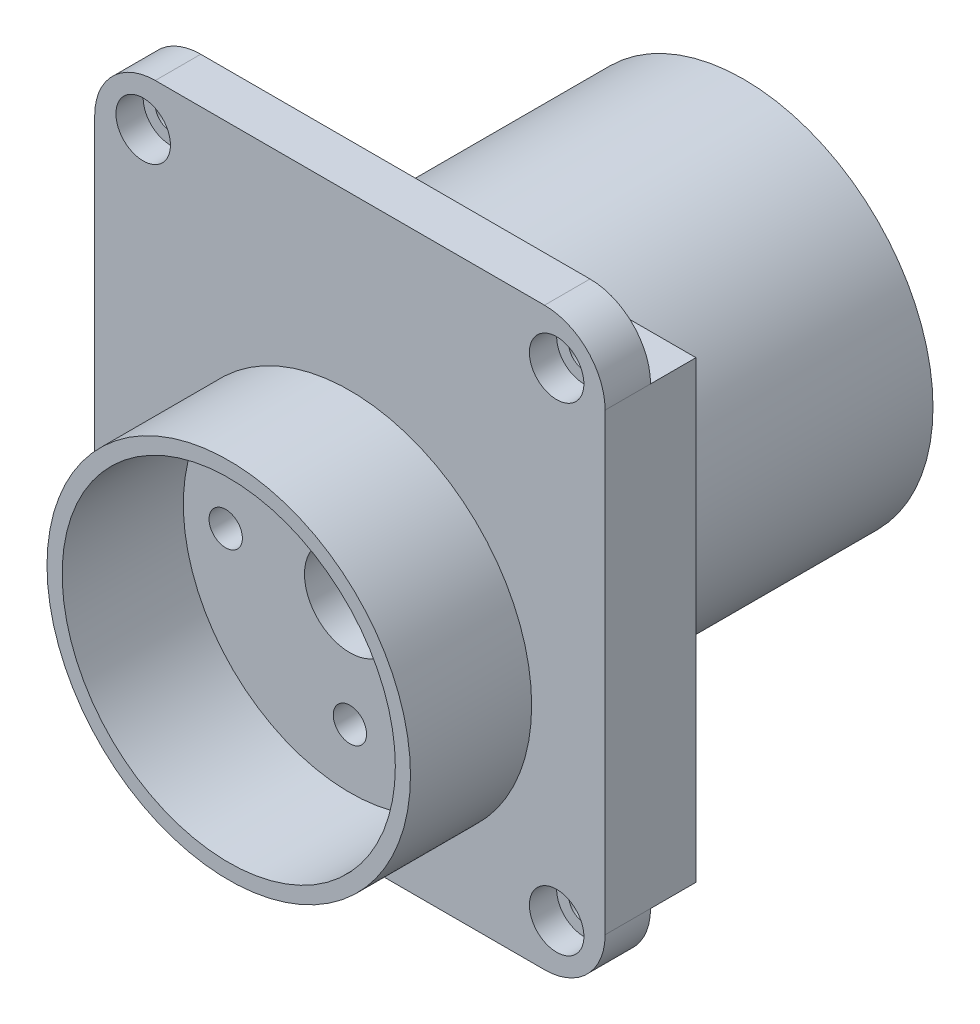
SolidWorks part; units mm, degrees
material "ABS"
ref_plane "Płaszczyzna przednia" through (0, 0, 0) normal (0, 0, 1) x (1, 0, 0)
ref_plane "Płaszczyzna górna" through (0, 0, 0) normal (0, 1, 0) x (1, 0, 0)
ref_plane "Płaszczyzna prawa" through (0, 0, 0) normal (1, 0, 0) x (0, 0, -1)
sketch "Szkic1" plane through (0, 0, 0) normal (0, 0, 1) x (1, 0, 0)
  line L0 (-24.531, 0) -> (41.5648, 0) construction
  line L1 (0, 25.1144) -> (0, -24.8112) construction
  line L2 (-16.85, 0) -> (-16.85, -14.7)
  line L3 (-16.85, -14.7) -> (0, -14.7)
  line L4 (0, -14.7) -> (16.85, -14.7)
  line L5 (16.85, -14.7) -> (16.85, 23.3)
  line L6 (16.85, 23.3) -> (-16.85, 23.3)
  line L7 (-16.85, 23.3) -> (-16.85, 0)
  line L8 (-13.65, 27.1146) -> (-13.65, -20.6837) construction
  line L9 (13.65, 25.9393) -> (13.65, -20.0568) construction
  circle A0 centre (0, 0) radius 3
  circle A1 centre (-8.2, 0) radius 1.1
  circle A2 centre (8.2, 0) radius 1.1
  circle A3 centre (0, 7.1) radius 1.1
  circle A4 centre (0, -7.1) radius 1.1
  circle A5 centre (-13.65, 20.1) radius 1
  circle A6 centre (13.65, 20.1) radius 1
  circle A7 centre (13.65, -11.5) radius 1
  circle A8 centre (-13.65, -11.5) radius 1
  dimension "D3" = 6
  dimension "D9" = 2.2
  dimension "D10" = 2.2
  dimension "D11" = 2.2
  dimension "D12" = 2.2
  dimension "D19" = 2
  dimension "D20" = 2
  dimension "D21" = 2
  dimension "D22" = 2
  dimension "D1" = 38
  dimension "D2" = 33.7
  dimension "D4" = 14.7
  dimension "D5" = 8.2
  dimension "D6" = 8.2
  dimension "D7" = 7.1
  dimension "D8" = 7.1
  dimension "D13" = 3.2
  dimension "D14" = 3.2
  dimension "D15" = 3.2
  dimension "D16" = 3.2
  dimension "D17" = 3.2
  dimension "D18" = 3.2
extrude "Dodanie-wyciągnięcie1" add sketch "Szkic1" along normal blind 3
sketch "Szkic2" plane through (0, 0, 3) normal (0, 0, 1) x (1, 0, 0)
  circle A0 centre (0, 0) radius 12
  circle A1 centre (0, 0) radius 11
  dimension "D1" = 24
  dimension "D2" = 22
extrude "Dodanie-wyciągnięcie2" add sketch "Szkic2" along normal blind 8
sketch "Szkic3" plane through (0, 0, 0) normal (0, 0, -1) x (-1, 0, 0)
  line L0 (-15.85, 27.4391) -> (-15.85, -18.66)
  line L1 (15.85, 26.9614) -> (15.85, -19.914)
  line L2 (-25.3784, -13.7) -> (25.1395, -13.7)
  line L3 (-22.9301, 22.3) -> (20.3027, 22.3)
  line L4 (-16.85, 23.3) -> (16.85, 23.3) construction
  line L5 (-16.85, -14.7) -> (-16.85, 23.3) construction
  line L6 (16.85, 23.3) -> (16.85, -14.7) construction
  line L7 (16.85, -14.7) -> (-16.85, -14.7) construction
  line L8 (-16.85, -14.7) -> (-16.85, 23.3)
  line L9 (-16.85, 23.3) -> (16.85, 23.3)
  line L10 (16.85, 23.3) -> (16.85, -14.7)
  line L11 (16.85, -14.7) -> (-16.85, -14.7)
  circle A0 centre (-13.65, 20.1) radius 3.2
  circle A1 centre (13.65, 20.1) radius 3.2
  circle A2 centre (-13.65, -11.5) radius 3.2
  circle A3 centre (13.65, -11.5) radius 3.2
  circle M9 centre (0, 0) radius 3
  circle M10 centre (8.2, 0) radius 1.1
  circle M11 centre (-8.2, 0) radius 1.1
  circle M12 centre (0, 7.1) radius 1.1
  circle M13 centre (0, -7.1) radius 1.1
  dimension "D5" = 6.4
  dimension "D6" = 6.4
  dimension "D7" = 6.4
  dimension "D8" = 6.4
  dimension "D1" = 1
  dimension "D2" = 1
  dimension "D3" = 1
  dimension "D4" = 1
extrude "Wytnij-wyciągnięcie1" cut sketch "Szkic3" against normal blind 1 contours A3 L1 A1 L3 A0 L0 A2 L2 M9 M11 M13 M12 M10
sketch "Szkic4" plane through (0, 0, 3) normal (0, 0, 1) x (1, 0, 0)
  circle A0 centre (-13.65, 20.1) radius 1.8
  circle A1 centre (13.65, 20.1) radius 1.8
  circle A2 centre (13.65, -11.5) radius 1.8
  circle A3 centre (-13.65, -11.5) radius 1.8
  dimension "D1" = 3.6
  dimension "D2" = 3.6
  dimension "D3" = 3.6
  dimension "D4" = 3.6
extrude "Wytnij-wyciągnięcie2" cut sketch "Szkic4" against normal blind 1.8
fillet "Zaokrąglenie1" radius 4 4 edges at (-16.85, 23.3, 1.5) (-16.85, -14.7, 1.5) (16.85, -14.7, 1.5) (16.85, 23.3, 1.5)
sketch "Sketch1" plane through (0, 0, 0) normal (0, 0, -1) x (-1, 0, 0)
  line L1 (-16.85, -10.7) -> (16.85, -10.7)
  line L2 (-16.85, -10.7) -> (-16.85, 19.3)
  line L3 (-16.85, 19.3) -> (16.85, 19.3)
  line L4 (16.85, -10.7) -> (16.85, 19.3)
extrude "Boss-Extrude1" add sketch "Sketch1" along normal blind 3
sketch "Sketch2" plane through (0, 0, -3) normal (0, 0, -1) x (-1, 0, 0)
  line L0 (16.85, 19.3) -> (-16.85, -10.7) construction
  line L1 (-16.85, 19.3) -> (16.85, -10.7) construction
  circle A0 centre (0, 4.3) radius 10.5
  circle A1 centre (0, 4.3) radius 12.5
  dimension "D1" = 21
  dimension "D2" = 25
extrude "Boss-Extrude2" add sketch "Sketch2" along normal blind 20
